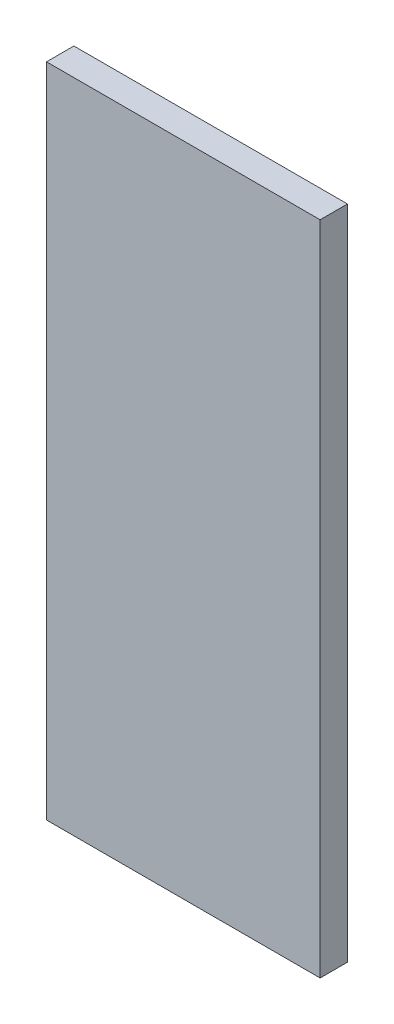
SolidWorks part; units mm, degrees
ref_plane "Front Plane" through (0, 0, 0) normal (0, 0, 1) x (1, 0, 0)
ref_plane "Top Plane" through (0, 0, 0) normal (0, 1, 0) x (1, 0, 0)
ref_plane "Right Plane" through (0, 0, 0) normal (1, 0, 0) x (0, 0, -1)
sketch "Sketch1" plane through (0, 0, 0) normal (0, 0, 1) x (1, 0, 0)
  line L0 (-1366.2105, -40.741) -> (-1366.2105, 111.659) construction
  line L1 (-1397.9605, -40.741) -> (-1334.4605, -40.741)
  line L2 (-1397.9605, -40.741) -> (-1397.9605, 111.659)
  line L3 (-1397.9605, 111.659) -> (-1334.4605, 111.659)
  line L4 (-1334.4605, -40.741) -> (-1334.4605, 111.659)
  line L5 (-1397.9605, -40.741) -> (-1397.9605, 111.659) construction
  line L6 (-1334.4605, 111.659) -> (-1334.4605, -40.741) construction
  dimension "D2" = 152.4
extrude "Boss-Extrude1" add sketch "Sketch1" along normal blind 6.35
ref_plane "Plane1" through (-1366.2105, 0, 0) normal (-1, 0, 0) x (0, 0, 1)
